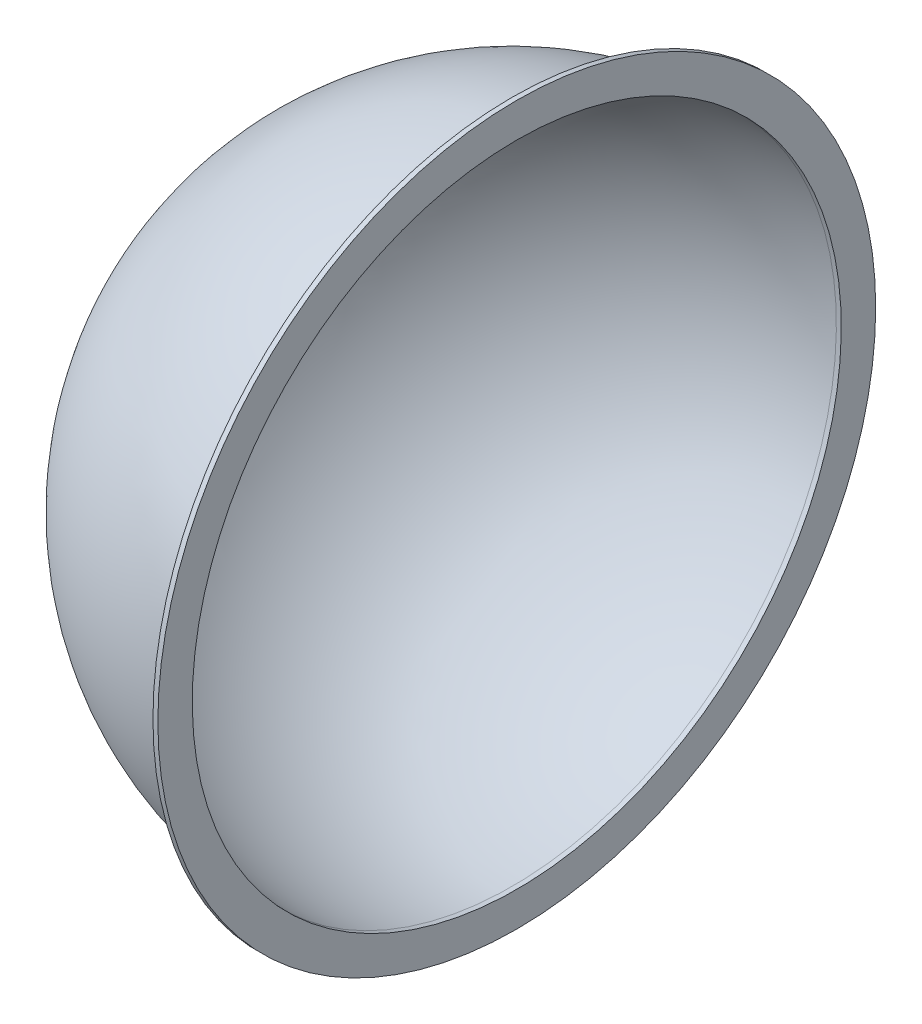
SolidWorks part; units mm, degrees
ref_plane "Front" through (0, 0, 0) normal (0, 0, 1) x (1, 0, 0)
ref_plane "Top" through (0, 0, 0) normal (0, 1, 0) x (1, 0, 0)
ref_plane "Right" through (0, 0, 0) normal (1, 0, 0) x (0, 0, -1)
sketch "Sketch1" plane through (0, 0, 0) normal (0, 0, 1) x (1, 0, 0)
  line L0 (-22.225, 138.1125) -> (-22.225, 149.225)
  line L1 (-22.225, 149.225) -> (-22.225, -82.55) construction
  line L2 (-22.225, 149.225) -> (-23.8125, 149.225)
  line L3 (-23.8125, 149.225) -> (-23.8125, 139.7)
  line L4 (-22.225, 33.3375) -> (-130.175, 33.3375) construction
  line L5 (-22.225, 138.1125) -> (-23.8125, 138.1125)
  line L6 (-128.5875, 33.3375) -> (-130.175, 33.3375)
  arc A0 (-23.8125, 139.7) -> (-130.175, 33.3375) centre (-23.8125, 33.3375) ccw
  arc A1 (-23.8125, 138.1125) -> (-128.5875, 33.3375) centre (-23.8125, 33.3375) ccw
  dimension "D1" = 1.5875
  dimension "D2" = 106.3625
  dimension "D3" = 1.5875
revolve "Revolve1" add sketch "Sketch1" angle 360 about L4
